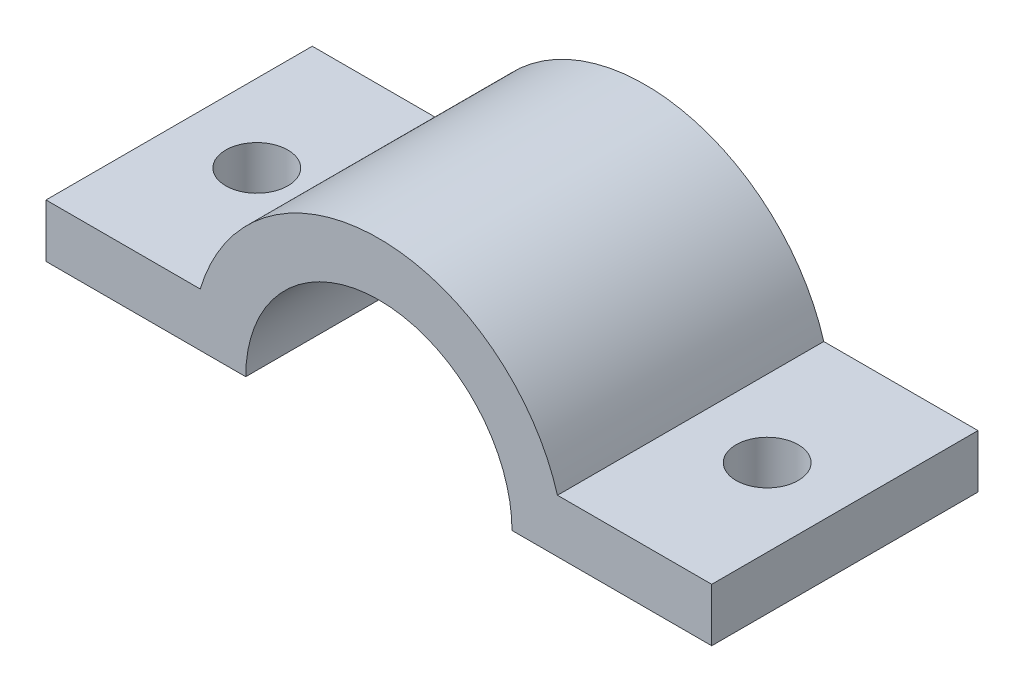
SolidWorks part; units mm, degrees
material "AISI 1020"
ref_plane "Plano frontal" through (0, 0, 0) normal (0, 0, 1) x (1, 0, 0)
ref_plane "Plano superior" through (0, 0, 0) normal (0, 1, 0) x (1, 0, 0)
ref_plane "Plano direito" through (0, 0, 0) normal (1, 0, 0) x (0, 0, -1)
sketch "Esboço1" plane through (0, 0, 0) normal (0, 0, 1) x (1, 0, 0)
  line L0 (15, 0) -> (37.5, 0)
  line L1 (37.5, 0) -> (37.5, 6)
  line L2 (37.5, 6) -> (20.1246, 6)
  line L3 (-15, 0) -> (-37.5, 0)
  line L4 (-37.5, 0) -> (-37.5, 6)
  line L5 (-37.5, 6) -> (-20.1246, 6)
  line L6 (0, 0) -> (0, 93.0486) construction
  arc A1 (15, 0) -> (-15, 0) centre (0, 0) ccw
  arc A2 (20.1246, 6) -> (-20.1246, 6) centre (0, 0) ccw
  dimension "D2" = 21
  dimension "D3" = 15
  dimension "D1" = 6
  dimension "D4" = 75
extrude "Ressalto-extrusão1" add sketch "Esboço1" along normal mid plane 30
hole_wizard "Furo de diâmetro Ø7.0 (7)1" positions "Esboço3" profile "Esboço2" hole size "Ø7.0" standard "ISO" end condition through all
sketch "Esboço3" plane through (0, 6, 0) normal (0, 1, 0) x (1, 0, 0)
  line L0 (0, 0) -> (0, 23.7705) construction
  line L3 (-55.8301, 0) -> (47.7847, 0) construction
  point P14 (-28.75, 0)
  point P16 (28.75, 0)
  dimension "D1" = 57.5
sketch "Esboço2" plane through (-28.75, 6, 0) normal (1, 0, 0) x (0, 0, 1)
  line L0 (0, 0) -> (0, 6)
  line L1 (0, 6) -> (3.5, 6)
  line L2 (3.5, 6) -> (3.5, 0)
  line L5 (3.5, 0) -> (0, 0)
  line L11 (0, -6.35) -> (0, 107.95) construction
  dimension "Thru Hole Dia." = 7
  dimension "Thru Hole Depth" = 6
